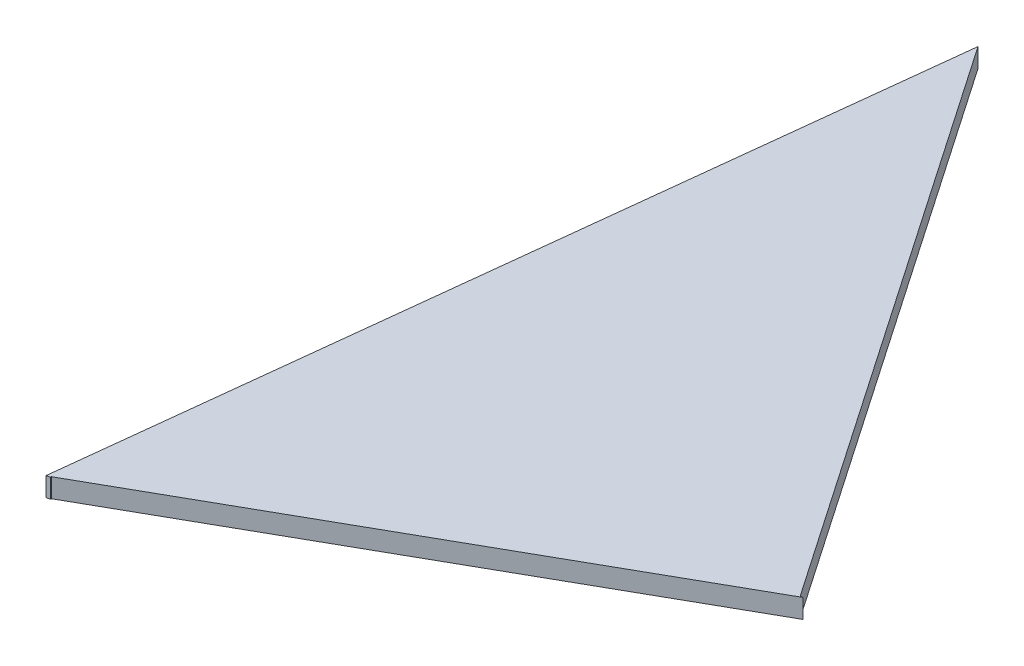
SolidWorks part; units mm, degrees
ref_plane "Plan de face" through (0, 0, 0) normal (0, 0, 1) x (1, 0, 0)
ref_plane "Plan de dessus" through (0, 0, 0) normal (0, 1, 0) x (1, 0, 0)
ref_plane "Plan de droite" through (0, 0, 0) normal (1, 0, 0) x (0, 0, -1)
sketch "Esquisse1" plane through (0, 0, 0) normal (0, 1, 0) x (1, 0, 0)
  line L3 (50.6904, 28.591) -> (50.4343, 28.5627)
  line L4 (50.4343, 28.5627) -> (9.8942, 87.729)
  line L5 (9.8942, 87.729) -> (0, 0)
  line L6 (0, 0) -> (0.3775, 0.0854)
  line L7 (0.3775, 0.0854) -> (0.3775, 0.1786)
  line L8 (0.3775, 0.1786) -> (50.6904, 28.591)
  point P6 (0, 0)
extrude "Boss.-Extru.1" add sketch "Esquisse1" along normal blind 2
